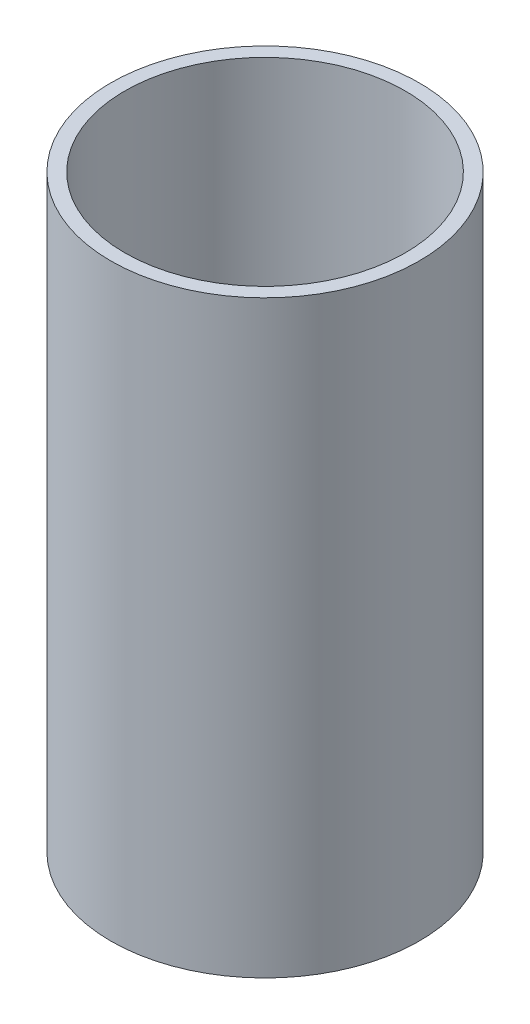
SolidWorks part; units mm, degrees
material "Corrugated Paper"
ref_plane "Front Plane" through (0, 0, 0) normal (0, 0, 1) x (1, 0, 0)
ref_plane "Top Plane" through (0, 0, 0) normal (0, 1, 0) x (1, 0, 0)
ref_plane "Right Plane" through (0, 0, 0) normal (1, 0, 0) x (0, 0, -1)
sketch "Sketch1" plane through (0, 0, 0) normal (0, 1, 0) x (1, 0, 0)
  circle A0 centre (0, 0) radius 38.1
  circle A1 centre (0, 0) radius 41.9
  dimension "D1" = 83.8
  dimension "D2" = 76.2
extrude "Boss-Extrude1" add sketch "Sketch1" along normal blind 160
